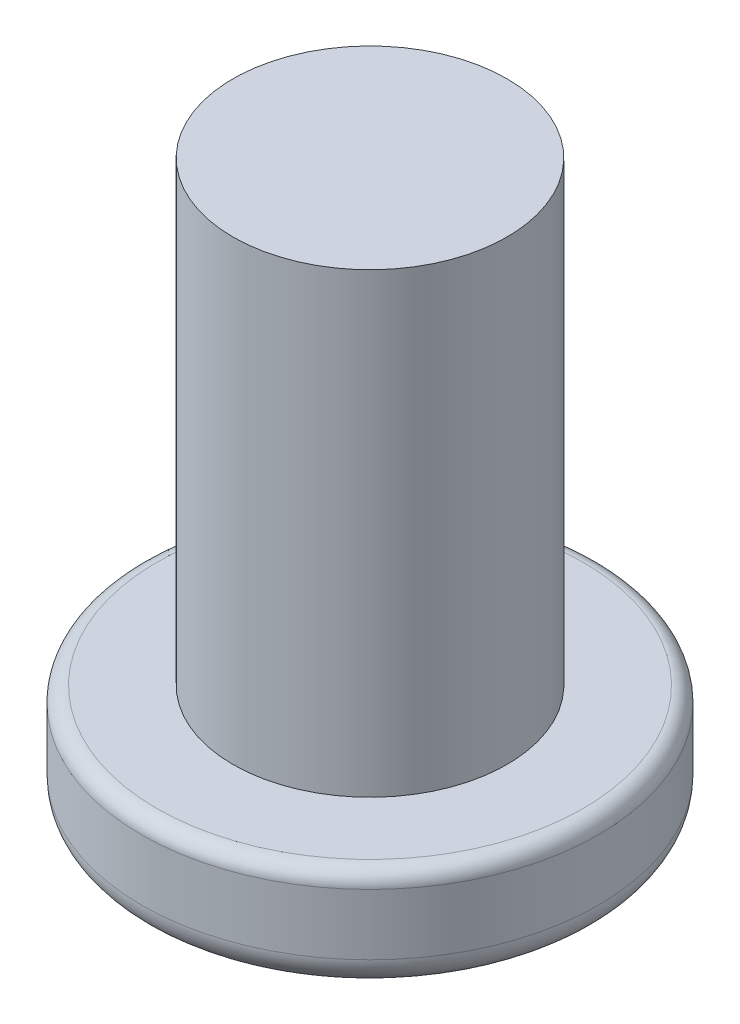
SolidWorks part; units mm, degrees
ref_plane "Front Plane" through (0, 0, 0) normal (0, 0, 1) x (1, 0, 0)
ref_plane "Top Plane" through (0, 0, 0) normal (0, 1, 0) x (1, 0, 0)
ref_plane "Right Plane" through (0, 0, 0) normal (1, 0, 0) x (0, 0, -1)
sketch "Sketch2" plane through (0, 0, 0) normal (0, 1, 0) x (1, 0, 0)
  circle A0 centre (0, 0) radius 7.5
  dimension "D1" = 15
extrude "Boss-Extrude1" add sketch "Sketch2" along normal blind 3.5
sketch "Sketch3" plane through (0, 3.5, 0) normal (0, 1, 0) x (1, 0, 0)
  circle A0 centre (0, 0) radius 4.5
  dimension "D1" = 9
extrude "Boss-Extrude2" add sketch "Sketch3" along normal blind 15
fillet "Fillet1" radius 1 1 edges at (0, 0, 7.5)
fillet "Fillet2" radius 0.5 1 edges at (0, 3.5, 7.5)
